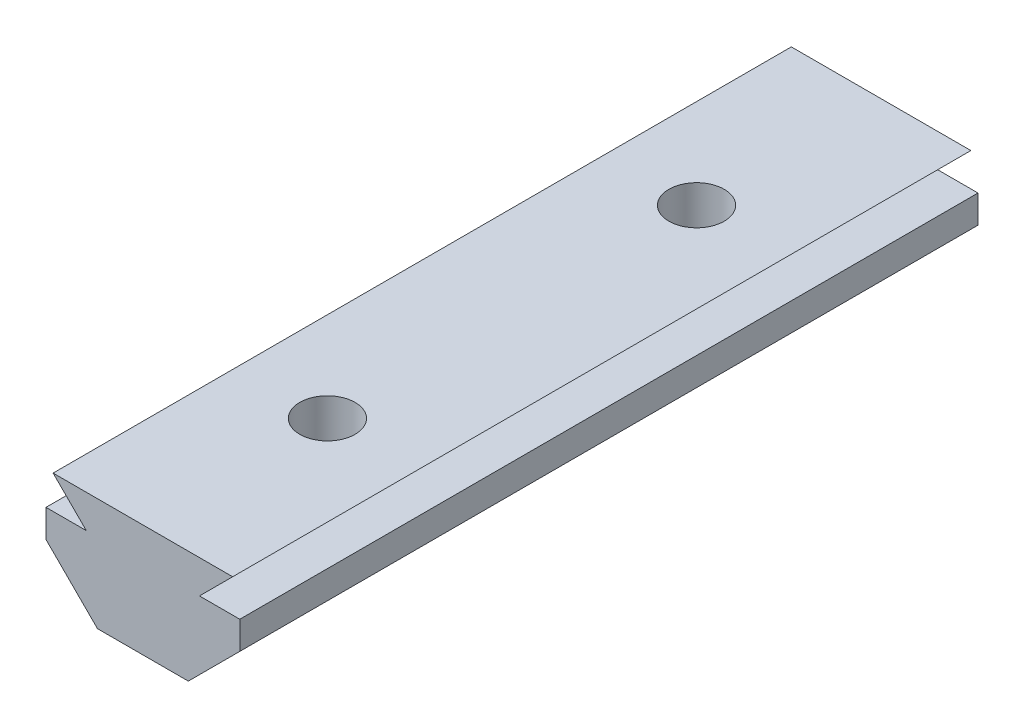
SolidWorks part; units mm, degrees
ref_plane "Front Plane" through (0, 0, 0) normal (0, 0, 1) x (1, 0, 0)
ref_plane "Top Plane" through (0, 0, 0) normal (0, 1, 0) x (1, 0, 0)
ref_plane "Right Plane" through (0, 0, 0) normal (1, 0, 0) x (0, 0, -1)
sketch "Sketch1" plane through (0, 0, 0) normal (0, 0, 1) x (1, 0, 0)
  line L0 (-2.4607, 0) -> (2.4607, 0)
  line L1 (2.4607, 0) -> (5.25, 2.7893)
  line L2 (-2.4607, 0) -> (-5.25, 2.7893)
  line L3 (-5.25, 2.7893) -> (-5.25, 4.3)
  line L4 (5.25, 2.7893) -> (5.25, 4.3)
  line L5 (-5.25, 4.3) -> (-3.065, 4.3)
  line L6 (5.25, 4.3) -> (3.065, 4.3)
  line L7 (-3.065, 4.3) -> (-4.865, 6.1)
  line L8 (3.065, 4.3) -> (4.865, 6.1)
  line L9 (4.865, 6.1) -> (-4.865, 6.1)
  point P4 (0, 0)
  dimension "D1" = 6.13
  dimension "D2" = 10.5
  dimension "D3" = 4.3
  dimension "D4" = 4.3
  dimension "D5" = 1.8
  dimension "D6" = 1.8
extrude "Boss-Extrude1" add sketch "Sketch1" along normal blind 40
sketch "Sketch2" plane through (0, 6.1, 0) normal (0, 1, 0) x (1, 0, 0)
  line L0 (0, 0) -> (0, -40) construction
  line L1 (4.865, 0) -> (-4.865, 0) construction
  line L2 (4.865, -40) -> (-4.865, -40) construction
  circle A0 centre (0, -30) radius 1.5
  circle A1 centre (0, -10) radius 1.5
  dimension "D3" = 3
  dimension "D1" = 10
  dimension "D2" = 10
extrude "Cut-Extrude1" cut sketch "Sketch2" against normal through all
sketch "Sketch3" plane through (0, 6.1, 0) normal (0, 1, 0) x (1, 0, 0)
  circle A0 centre (0, -10) radius 3
  circle A1 centre (0, -30) radius 3
  dimension "D1" = 6
sketch "Sketch5" plane through (0, 0, 0) normal (0, -1, 0) x (-1, 0, 0)
  line L1 (-3.2332, -10) -> (-1.6166, -12.8)
  line L2 (-1.6166, -12.8) -> (1.6166, -12.8)
  line L3 (1.6166, -12.8) -> (3.2332, -10)
  line L4 (3.2332, -10) -> (1.6166, -7.2)
  line L5 (1.6166, -7.2) -> (-1.6166, -7.2)
  line L6 (-1.6166, -7.2) -> (-3.2332, -10)
  line L7 (-3.2332, -30) -> (-1.6166, -32.8)
  line L8 (-1.6166, -32.8) -> (1.6166, -32.8)
  line L9 (1.6166, -32.8) -> (3.2332, -30)
  line L10 (3.2332, -30) -> (1.6166, -27.2)
  line L11 (1.6166, -27.2) -> (-1.6166, -27.2)
  line L12 (-1.6166, -27.2) -> (-3.2332, -30)
  circle A0 centre (0, -10) radius 2.8 construction
  circle A1 centre (0, -30) radius 2.8 construction
  dimension "D1" = 5.6
extrude "Cut-Extrude3" cut sketch "Sketch5" against normal blind 3
